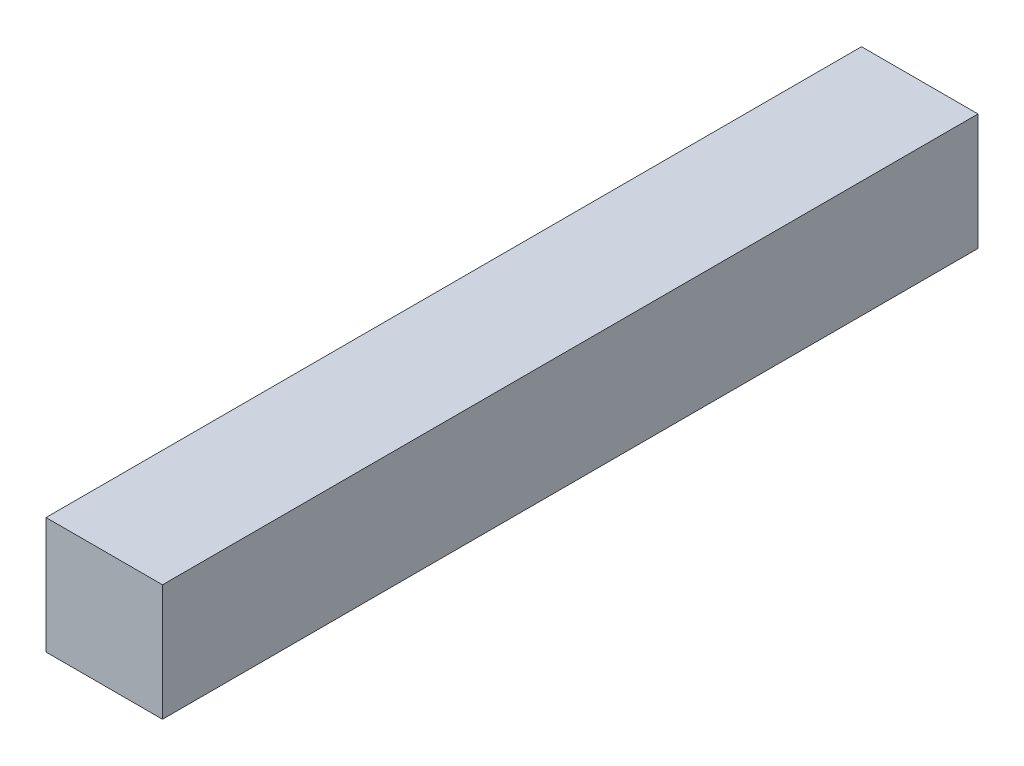
SolidWorks part; units mm, degrees
ref_plane "Front Plane" through (0, 0, 0) normal (0, 0, 1) x (1, 0, 0)
ref_plane "Top Plane" through (0, 0, 0) normal (0, 1, 0) x (1, 0, 0)
ref_plane "Right Plane" through (0, 0, 0) normal (1, 0, 0) x (0, 0, -1)
sketch "Sketch1" plane through (0, 0, 0) normal (0, 0, 1) x (1, 0, 0)
  line L1 (-49.6175, 18.1931) -> (-39.6175, 18.1931)
  line L2 (-49.6175, 18.1931) -> (-49.6175, 8.1931)
  line L3 (-49.6175, 8.1931) -> (-39.6175, 8.1931)
  line L4 (-39.6175, 18.1931) -> (-39.6175, 8.1931)
extrude "Boss-Extrude1" add sketch "Sketch1" along normal blind 70
